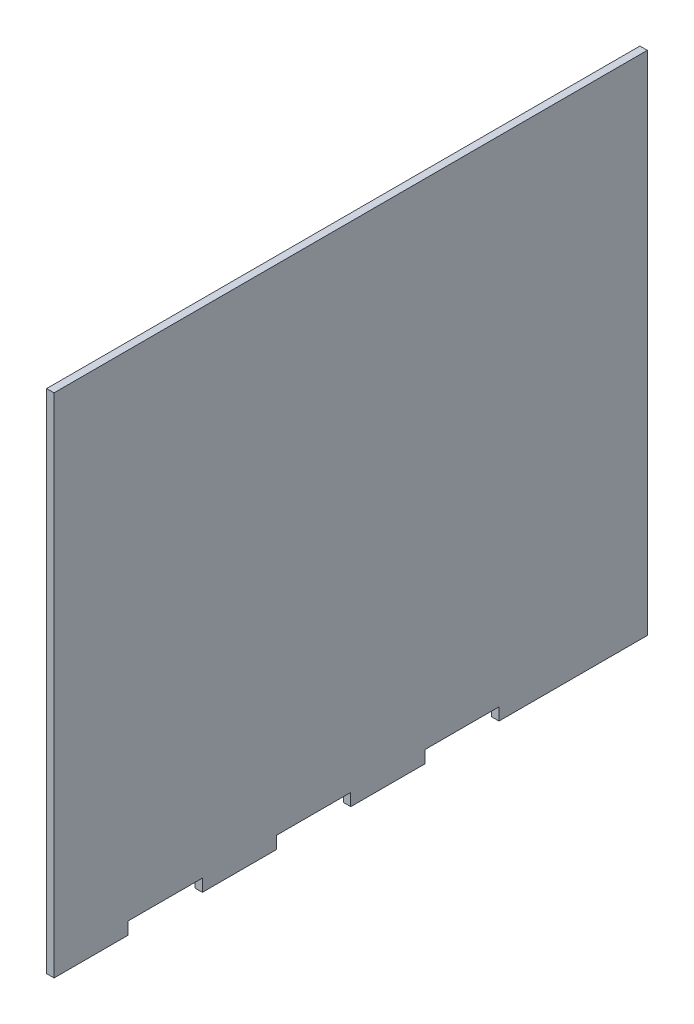
SolidWorks part; units mm, degrees
ref_plane "Front Plane" through (0, 0, 0) normal (0, 0, 1) x (1, 0, 0)
ref_plane "Top Plane" through (0, 0, 0) normal (0, 1, 0) x (1, 0, 0)
ref_plane "Right Plane" through (0, 0, 0) normal (1, 0, 0) x (0, 0, -1)
sketch "Sketch1" plane through (0, 0, 0) normal (1, 0, 0) x (0, 0, -1)
  line L1 (-120, 102.5) -> (120, 102.5)
  line L2 (-120, 102.5) -> (-120, -102.5)
  line L3 (-120, -102.5) -> (120, -102.5)
  line L4 (120, 102.5) -> (120, -102.5)
  line L5 (-120, 102.5) -> (120, -102.5) construction
  line L6 (-120, -102.5) -> (120, 102.5) construction
  point P0 (0, 0)
  dimension "D1" = 240
  dimension "D2" = 205
extrude "Boss-Extrude1" add sketch "Sketch1" along normal blind 3
sketch "Sketch2" plane through (3, 0, 0) normal (1, 0, 0) x (0, 0, -1)
  line L0 (-90, -102.5) -> (-90, -97.5)
  line L1 (-120, -102.5) -> (120, -102.5) construction
  line L2 (-90, -97.5) -> (-60, -97.5)
  line L3 (-60, -97.5) -> (-60, -102.5)
  line L4 (-60, -102.5) -> (-90, -102.5)
  line L5 (-30, -102.5) -> (-30, -97.5)
  line L6 (-30, -97.5) -> (0, -97.5)
  line L7 (0, -97.5) -> (0, -102.5)
  line L8 (0, -102.5) -> (-30, -102.5)
  line L9 (30, -102.5) -> (30, -97.5)
  line L10 (30, -97.5) -> (60, -97.5)
  line L11 (60, -97.5) -> (60, -102.5)
  line L12 (60, -102.5) -> (30, -102.5)
  line L13 (-120, 102.5) -> (-120, -102.5) construction
  dimension "D1" = 30
  dimension "D2" = 30
  dimension "D3" = 30
  dimension "D4" = 30
  dimension "D5" = 5
extrude "Cut-Extrude1" cut sketch "Sketch2" against normal blind 3
